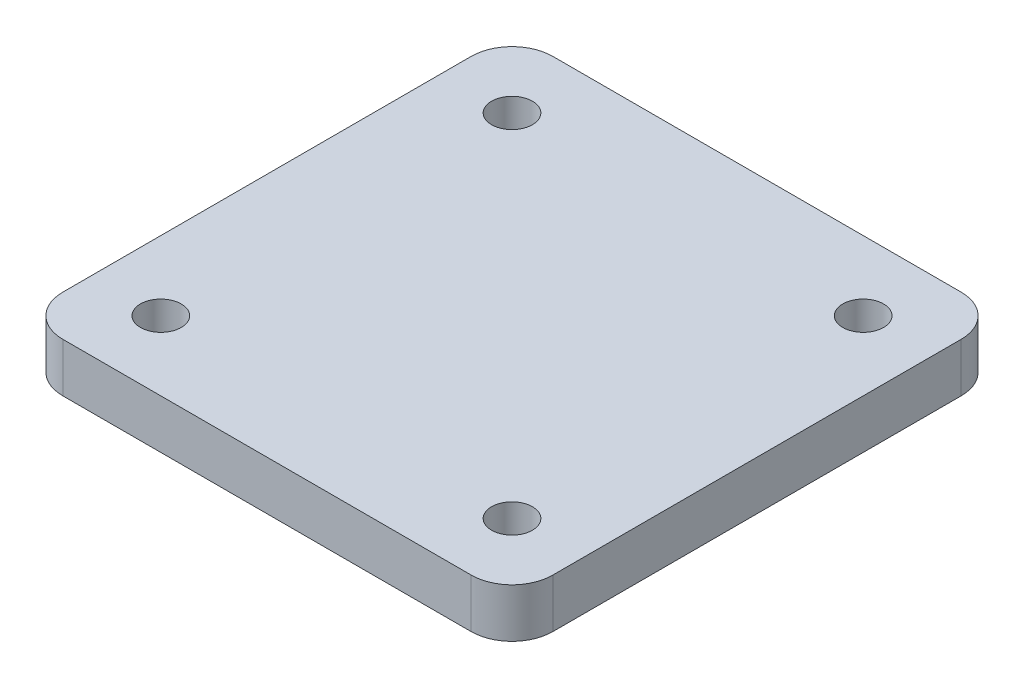
SolidWorks part; units mm, degrees
material "1.0037 (S235JR)"
ref_plane "Front Plane" through (0, 0, 0) normal (0, 0, 1) x (1, 0, 0)
ref_plane "Top Plane" through (0, 0, 0) normal (0, 1, 0) x (1, 0, 0)
ref_plane "Right Plane" through (0, 0, 0) normal (1, 0, 0) x (0, 0, -1)
sketch "Sketch1" plane through (0, 0, 0) normal (0, 1, 0) x (1, 0, 0)
  line L1 (-5, 0) -> (-55, 0)
  line L2 (0, 5) -> (0, 55)
  line L3 (-5, 60) -> (-55, 60)
  line L4 (-60, 5) -> (-60, 55)
  circle A0 centre (-51.5, 51.5) radius 2.5
  circle A1 centre (-8.5, 51.5) radius 2.5
  circle A2 centre (-8.5, 8.5) radius 2.5
  circle A3 centre (-51.5, 8.5) radius 2.5
  arc A4 (-55, 0) -> (-60, 5) centre (-55, 5) cw
  arc A5 (-5, 0) -> (0, 5) centre (-5, 5) ccw
  arc A6 (0, 55) -> (-5, 60) centre (-5, 55) ccw
  arc A7 (-55, 60) -> (-60, 55) centre (-55, 55) ccw
  point P15 (-60, 0)
  point P18 (0, 0)
  point P21 (0, 60)
  point P24 (-60, 60)
  dimension "D3" = 5
  dimension "D4" = 43
  dimension "D5" = 43
  dimension "D6" = 8.5
  dimension "D7" = 8.5
  dimension "D8" = 5
  dimension "D1" = 60
  dimension "D2" = 60
extrude "Boss-Extrude1" add sketch "Sketch1" along normal blind 6
